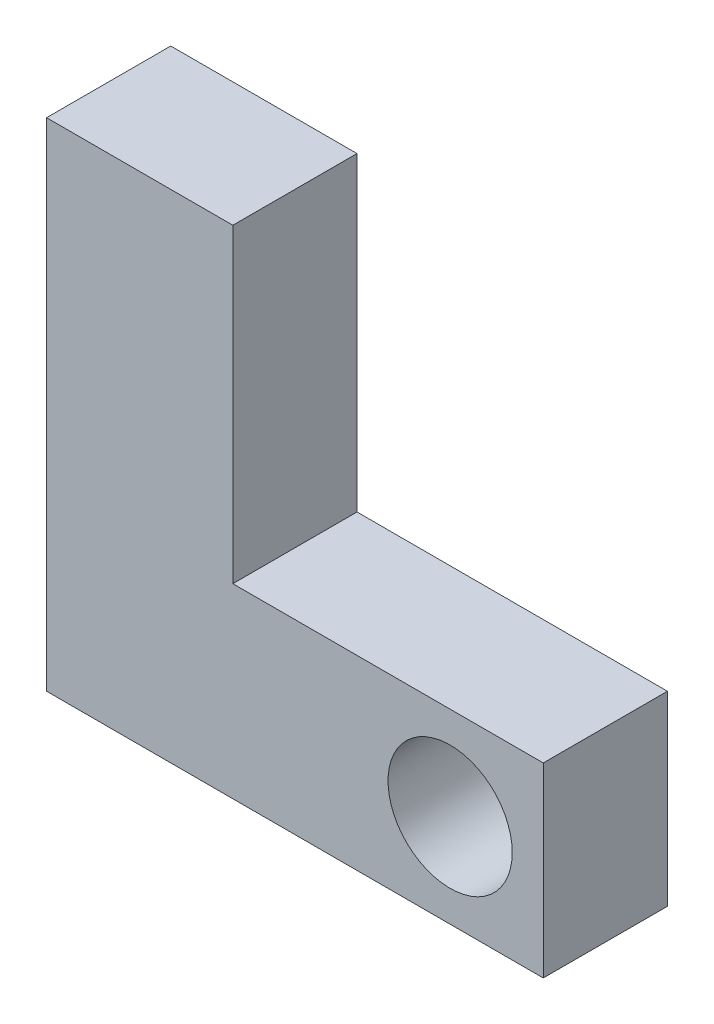
SolidWorks part; units mm, degrees
ref_plane "Front Plane" through (0, 0, 0) normal (0, 0, 1) x (1, 0, 0)
ref_plane "Top Plane" through (0, 0, 0) normal (0, 1, 0) x (1, 0, 0)
ref_plane "Right Plane" through (0, 0, 0) normal (1, 0, 0) x (0, 0, -1)
sketch "Sketch1" plane through (0, 0, 0) normal (0, 0, 1) x (1, 0, 0)
  line L1 (-19.5012, 6.2908) -> (-9.9762, 6.2908)
  line L2 (-19.5012, 6.2908) -> (-19.5012, -19.1092)
  line L3 (-19.5012, -19.1092) -> (5.8988, -19.1092)
  line L4 (5.8988, -9.5842) -> (5.8988, -19.1092)
  line L7 (5.8988, -9.5842) -> (-9.9762, -9.5842)
  line L8 (-9.9762, 6.2908) -> (-9.9762, -9.5842)
  dimension "D1" = 9.525
  dimension "D2" = 25.4
  dimension "D3" = 25.4
extrude "Extrude1" add sketch "Sketch1" along normal blind 6.35
sketch "Sketch2" plane through (0, 0, 6.35) normal (0, 0, 1) x (1, 0, 0)
  line L0 (-19.5012, -19.1092) -> (5.8988, -19.1092) construction
  line L1 (5.8988, -19.1092) -> (5.8988, -9.5842) construction
  circle A0 centre (1.1363, -14.3467) radius 3.175
  dimension "D3" = 6.35
  dimension "D1" = 4.7625
  dimension "D2" = 4.7625
extrude "Cut-Extrude1" cut sketch "Sketch2" against normal through all
sketch "Sketch3" plane through (-19.5012, 0, 0) normal (-1, 0, 0) x (0, 0, 1)
  line L0 (0, 6.2908) -> (0, -19.1092) construction
  line L1 (6.35, 6.2908) -> (0, 6.2908) construction
  circle A0 centre (3.175, -6.4092) radius 1.6096
  dimension "D1" = 3.175
  dimension "D2" = 12.7
extrude "Cut-Extrude2" cut sketch "Sketch3" against normal blind 6.35
